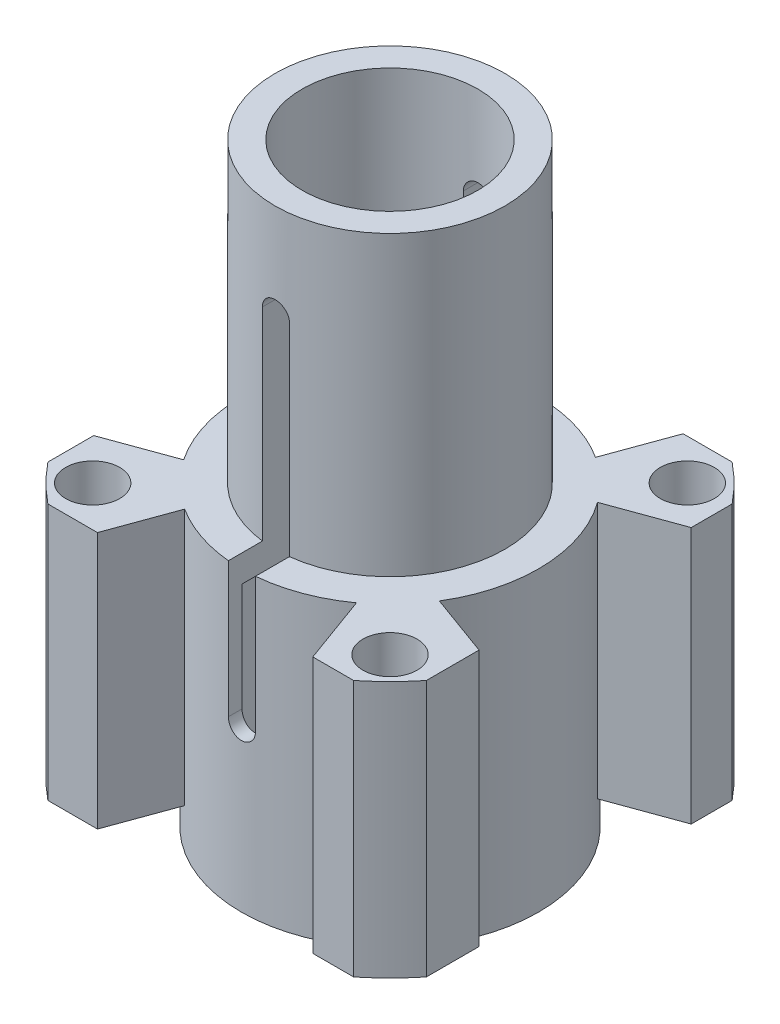
SolidWorks part; units mm, degrees
ref_plane "Plan de face" through (0, 0, 0) normal (0, 0, 1) x (1, 0, 0)
ref_plane "Plan de dessus" through (0, 0, 0) normal (0, 1, 0) x (1, 0, 0)
ref_plane "Plan de droite" through (0, 0, 0) normal (1, 0, 0) x (0, 0, -1)
sketch "Esquisse1" plane through (0, 0, 0) normal (0, 0, 1) x (1, 0, 0)
  line L0 (-6.5, 20) -> (-6.5, 44)
  line L1 (-11, 22) -> (-11, 0)
  line L2 (-11, 0) -> (-10, 0)
  line L3 (-10, 0) -> (-10, 20)
  line L4 (-8.5, 22) -> (-8.5, 44)
  line L5 (-10, 20) -> (-6.5, 20)
  line L6 (-11, 22) -> (-8.5, 22)
  line L7 (-8.5, 44) -> (-6.5, 44)
  line L8 (-11, 22) -> (-10, 22) construction
  line L9 (-10, 44) -> (-6.5, 44) construction
  line L10 (-11, 20) -> (-10, 20) construction
  line L11 (0, 0) -> (0, 15.3273) construction
  line L12 (0, 0) -> (0, 44) construction
  line L15 (-10, 20) -> (-6.5, 20) construction
  line L16 (-8.5, 0) -> (-8.5, 15.3273) construction
  line L18 (-6.5, 0) -> (-6.5, 15.3273) construction
  dimension "D1" = 22
  dimension "D2" = 1
  dimension "D3" = 20
  dimension "D4" = 22
  dimension "D5" = 2
  dimension "D6" = 10
  dimension "D7" = 13
revolve "Révolution1" add sketch "Esquisse1" angle 360 about L12
sketch "Esquisse2" plane through (0, 44, 0) normal (0, 1, 0) x (1, 0, 0)
  line L0 (-0.55, -6.4767) -> (-0.55, -9)
  line L3 (-0.55, -9) -> (0.55, -9)
  line L4 (0.55, -6.4767) -> (0.55, -9)
  arc A1 (-0.55, -6.4767) -> (0.55, -6.4767) centre (0, 0) ccw
sketch "Esquisse3" plane through (0, 22, 0) normal (0, 1, 0) x (1, 0, 0)
  line L0 (-11.3137, -14) -> (-7.6453, -14)
  line L1 (11.3137, 14) -> (7.6902, 14)
  line L2 (14, 11.3137) -> (14, 8.2881)
  line L3 (-14, -11.3137) -> (-14, -7.9241)
  line L4 (0, 0) -> (0, 4.2793) construction
  line L5 (0, 0) -> (-3.606, 0) construction
  line L6 (8.9187, 6.4387) -> (14, 8.2881)
  line L7 (14, -7.4114) -> (14, -11.3137)
  line L8 (6.4387, -8.9187) -> (8.2881, -14)
  line L9 (-5.9234, -9.269) -> (-7.6453, -14)
  line L10 (9.388, -5.7328) -> (14, -7.4114)
  line L11 (-9.1212, -6.1484) -> (-14, -7.9241)
  line L12 (-9.1212, 6.1484) -> (-14, 7.9241)
  line L13 (-6.1484, 9.1212) -> (-7.9241, 14)
  line L14 (5.9597, 9.2456) -> (7.6902, 14)
  line L15 (-7.9241, 14) -> (-11.3137, 14)
  line L16 (-14, 7.9241) -> (-14, 11.3137)
  line L17 (8.2881, -14) -> (11.3137, -14)
  line L18 (-11, 11) -> (11, -11) construction
  line L19 (11, 11) -> (-11, -11) construction
  line L20 (14, 11.3137) -> (14, -11.3137) construction
  line L21 (-11.3137, -14) -> (11.3137, -14) construction
  line L22 (-14, -11.3137) -> (-14, 11.3137) construction
  line L23 (-11.3137, 14) -> (11.3137, 14) construction
  circle A0 centre (11, 11) radius 2
  arc A1 (9.388, -5.7328) -> (8.9187, 6.4387) centre (0, 0) ccw
  circle A2 centre (-11, -11) radius 2
  circle A3 centre (-11, 11) radius 2
  circle A4 centre (11, -11) radius 2
  arc A5 (-14, -11.3137) -> (-11.3137, -14) centre (0, 0) ccw
  arc A6 (-11.3137, 14) -> (-14, 11.3137) centre (0, 0) ccw
  arc A7 (14, 11.3137) -> (11.3137, 14) centre (0, 0) ccw
  arc A8 (11.3137, -14) -> (14, -11.3137) centre (0, 0) ccw
  arc A9 (5.9597, 9.2456) -> (-6.1484, 9.1212) centre (0, 0) ccw
  arc A10 (-9.1212, 6.1484) -> (-9.1212, -6.1484) centre (0, 0) ccw
  circle A12 centre (0, 0) radius 10
  arc A13 (-5.9234, -9.269) -> (6.4387, -8.9187) centre (0, 0) ccw
  dimension "D1" = 20
  dimension "D2" = 11
  dimension "D3" = 4
  dimension "D7" = 18
  dimension "D4" = 22
  dimension "D5" = 28
  dimension "D6" = 28
  dimension "D8" = 4
  dimension "D9" = 14
  dimension "D10" = 14
extrude "Extrusion2" add sketch "Esquisse3" against normal blind 19
sketch "Esquisse4" plane through (0, 0, 14) normal (0, 0, 1) x (1, 0, 0)
  line L0 (0, 0) -> (0, 44) construction
  line L1 (8.5, 44) -> (-8.5, 44) construction
  line L2 (-11, 0) -> (11, 0) construction
  line L3 (-1, 37) -> (-1, 12)
  line L4 (1, 12) -> (1, 37)
  arc A0 (-1, 12) -> (1, 12) centre (0, 12) ccw
  arc A1 (1, 37) -> (-1, 37) centre (0, 37) ccw
  dimension "D1" = 2
  dimension "D2" = 12
  dimension "D3" = 7
extrude "Extrusion4" cut sketch "Esquisse4" against normal through all
